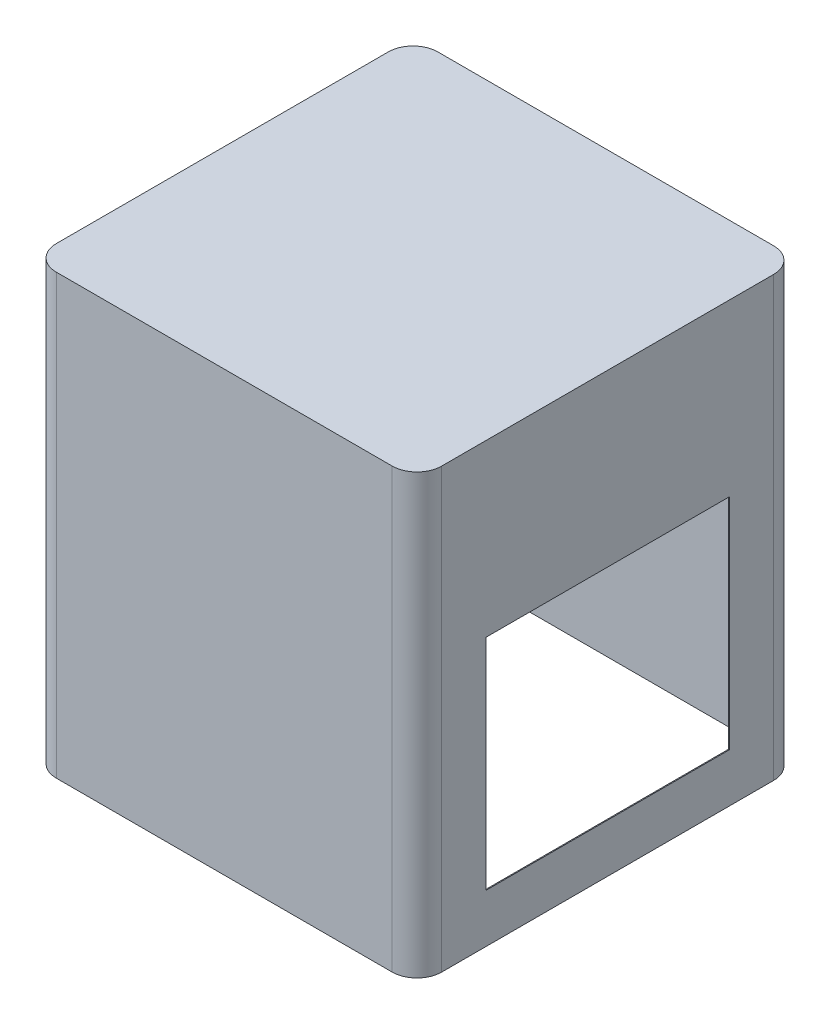
SolidWorks part; units mm, degrees
ref_plane "Front" through (0, 0, 0) normal (0, 0, 1) x (1, 0, 0)
ref_plane "Top" through (0, 0, 0) normal (0, 1, 0) x (1, 0, 0)
ref_plane "Right" through (0, 0, 0) normal (1, 0, 0) x (0, 0, -1)
sketch "Sketch1" plane through (0, 0, 0) normal (0, 1, 0) x (1, 0, 0)
  line L1 (197.8524, 195.8524) -> (-197.8524, 195.8524)
  line L2 (197.8524, 195.8524) -> (197.8524, -195.8524)
  line L3 (197.8524, -195.8524) -> (-197.8524, -195.8524)
  line L4 (-197.8524, 195.8524) -> (-197.8524, -195.8524)
  line L5 (197.8524, 195.8524) -> (-197.8524, -195.8524) construction
  line L6 (197.8524, -195.8524) -> (-197.8524, 195.8524) construction
  point P0 (0, 0)
  dimension "D1" = 395.7048
  dimension "D2" = 391.7048
extrude "Boss-Extrude1" add sketch "Sketch1" along normal blind 450
fillet "Fillet1" radius 25.4 4 edges at (197.8524, 225, -195.8524) (-197.8524, 225, -195.8524) (-197.8524, 225, 195.8524) (197.8524, 225, 195.8524)
shell "Shell1" thickness 0.9525
sketch "Sketch2" plane through (197.8524, 0, -2) normal (-1, 0, 0) x (0, 0, 1)
  line L0 (2, 50) -> (2, 0) construction
  line L1 (-123, 275) -> (127, 275)
  line L2 (-123, 275) -> (-123, 50)
  line L3 (-123, 50) -> (127, 50)
  line L4 (127, 275) -> (127, 50)
  line L7 (-168.4524, 0) -> (172.4524, 0) construction
  dimension "D1" = 250
  dimension "D2" = 225
  dimension "D3" = 50
extrude "Cut-Extrude1" cut sketch "Sketch2" along normal up to next
sketch "Sketch5" plane through (-197.8524, 0, 0) normal (-1, 0, 0) x (0, 0, 1)
  line L0 (34.5, 327.2329) -> (65.5, 296.2329) construction
  circle A0 centre (50, 311.7329) radius 11.5
  circle A1 centre (34.5, 327.2329) radius 1.75
  circle A2 centre (65.5, 327.2329) radius 1.75
  circle A3 centre (34.5, 296.2329) radius 1.75
  circle A4 centre (65.5, 296.2329) radius 1.75
  dimension "D1" = 23
  dimension "D2" = 3.5
  dimension "D3" = 31
  dimension "D4" = 31
